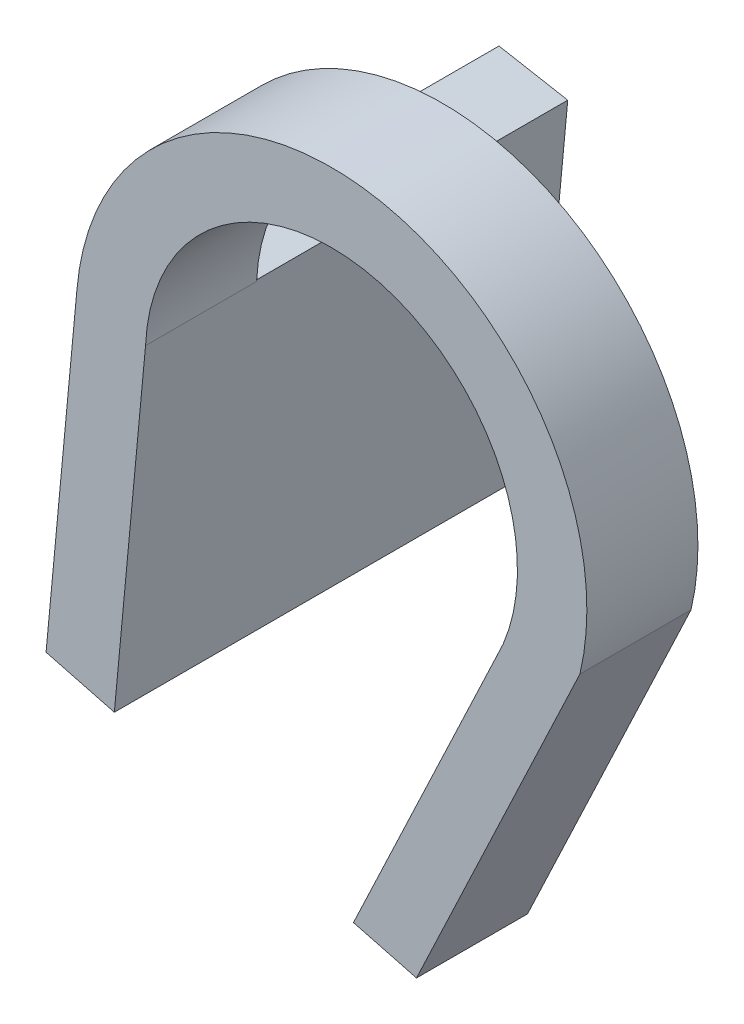
SolidWorks part; units mm, degrees
ref_plane "Front Plane" through (0, 0, 0) normal (0, 0, 1) x (1, 0, 0)
ref_plane "Top Plane" through (0, 0, 0) normal (0, 1, 0) x (1, 0, 0)
ref_plane "Right Plane" through (0, 0, 0) normal (1, 0, 0) x (0, 0, -1)
sketch "Sketch1" plane through (0, 0, 0) normal (0, 0, 1) x (1, 0, 0)
  line L0 (-16.7339, 0.7347) -> (-19.5437, -29.2653)
  line L1 (-19.5437, -29.2653) -> (1.9856, -34.8971)
  line L2 (1.9856, -34.8971) -> (14.8304, -7.786)
  line L3 (0.192, -0.8506) -> (14.8304, -7.786)
  line L4 (-16.7339, 0.7347) -> (0.192, -0.8506)
  line L5 (-22.9127, 2.0023) -> (-25.6907, -27.6574)
  line L6 (-25.6907, -27.6574) -> (7.6604, -36.3816)
  line L7 (7.6604, -36.3816) -> (22.3757, -5.3225)
  circle A0 centre (0, 0) radius 16.75
  circle A1 centre (0, 0) radius 23
  dimension "D2" = 33.5
  dimension "D12" = 0
  dimension "D13" = 46
  dimension "D1" = 0
  dimension "D3" = 16.75
  dimension "D4" = 16.75
  dimension "D5" = 0
  dimension "D6" = 30
  dimension "D7" = 90
  dimension "D10" = 90
  dimension "D11" = 30
  dimension "D14" = 23
  dimension "D15" = 23
  dimension "D16" = 180
  dimension "D17" = 180
  dimension "D19" = 160
extrude "Boss-Extrude3" add sketch "Sketch1" along normal blind 10 contours A1 L5 L6 L0 | A1 L0 A0 L2 L7 | A1 L2 L6 L7
sketch "Sketch2" plane through (0, 0, 0) normal (0, 0, -1) x (-1, 0, 0)
  line L0 (22.9127, 2.0023) -> (16.7206, 0.8761)
  line L1 (16.7206, 0.8761) -> (19.5437, -29.2653)
  line L2 (19.5437, -29.2653) -> (25.6907, -27.6574)
  line L3 (25.6907, -27.6574) -> (22.9127, 2.0023)
  line L4 (16.7339, 0.7347) -> (19.5437, -29.2653) construction
  line L5 (22.9127, 2.0023) -> (25.6907, -27.6574) construction
  line L7 (25.6907, -27.6574) -> (19.5437, -29.2653) construction
  point P4 (24.3017, -12.8275)
  point P11 (18.1388, -14.2653)
  dimension "D1" = 0
  dimension "D2" = 0
  dimension "D3" = 180
  dimension "D4" = 0
  dimension "D5" = 0
  dimension "D6" = 0
extrude "Boss-Extrude4" add sketch "Sketch2" along normal blind 28
